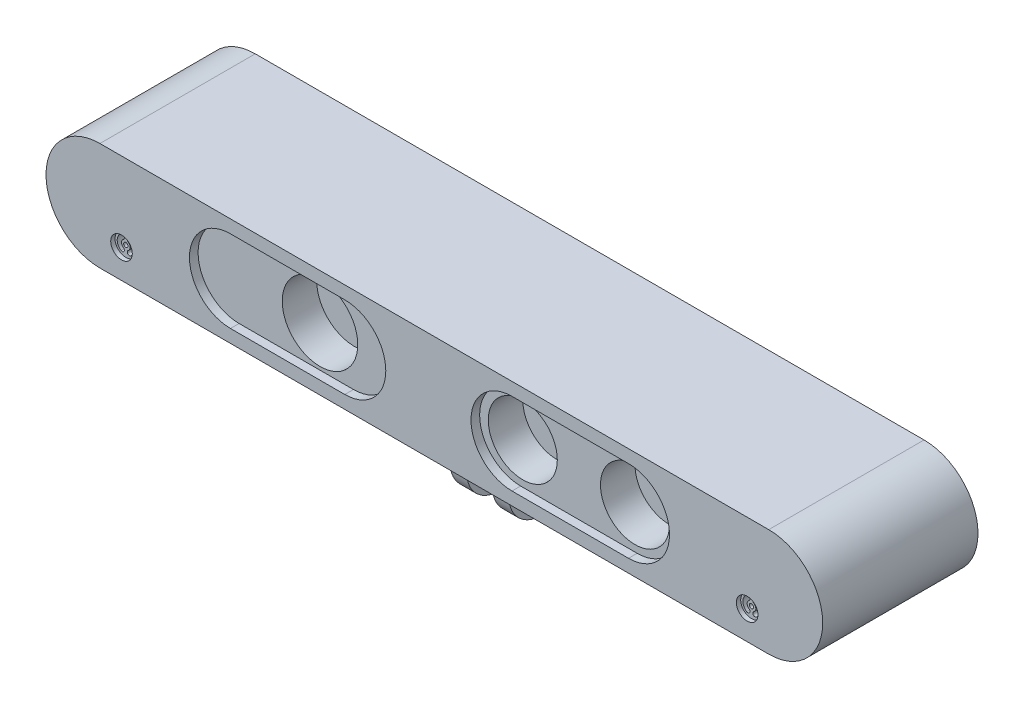
SolidWorks part; units mm, degrees
ref_plane "Front Plane" through (0, 0, 0) normal (0, 0, 1) x (1, 0, 0)
ref_plane "Top Plane" through (0, 0, 0) normal (0, 1, 0) x (1, 0, 0)
ref_plane "Right Plane" through (0, 0, 0) normal (1, 0, 0) x (0, 0, -1)
sketch "Sketch1" plane through (0, 0, 0) normal (0, 0, 1) x (1, 0, 0)
  line L0 (-77.5, 0) -> (77.5, 0) construction
  line L1 (-77.5, 12.5) -> (77.5, 12.5)
  line L2 (-77.5, -12.5) -> (77.5, -12.5)
  arc A0 (-77.5, 12.5) -> (-77.5, -12.5) centre (-77.5, 0) ccw
  arc A1 (77.5, -12.5) -> (77.5, 12.5) centre (77.5, 0) ccw
  point P3 (0, 0)
  dimension "D1" = 12.5
  dimension "D3" = 0
  dimension "D2" = 155
extrude "Boss-Extrude1" add sketch "Sketch1" against normal blind 36
sketch "Sketch3" plane through (0, 0, 0) normal (0, 0, 1) x (1, 0, 0)
  circle A0 centre (-28.5, 0) radius 8.75
  circle A1 centre (18.5, 0) radius 8
  circle A2 centre (44.5, 0) radius 8
  dimension "D1" = 17.5
  dimension "D4" = 16
  dimension "D7" = 16
  dimension "D2" = 28.5
  dimension "D3" = 0
  dimension "D5" = 47
  dimension "D6" = 73
  dimension "D8" = 0
  dimension "D9" = 0
extrude "Cut-Extrude1" cut sketch "Sketch3" against normal blind 10
sketch "Sketch4" plane through (0, 0, 0) normal (0, 0, 1) x (1, 0, 0)
  line L0 (-47.25, 0) -> (-20.75, 0) construction
  line L1 (-47.25, 9.5) -> (-20.75, 9.5)
  line L2 (-47.25, -9.5) -> (-20.75, -9.5)
  line L3 (18, 0) -> (45, 0) construction
  line L4 (18, 9.5) -> (45, 9.5)
  line L5 (18, -9.5) -> (45, -9.5)
  arc A0 (-47.25, 9.5) -> (-47.25, -9.5) centre (-47.25, 0) ccw
  arc A1 (-20.75, -9.5) -> (-20.75, 9.5) centre (-20.75, 0) ccw
  arc A2 (18, 9.5) -> (18, -9.5) centre (18, 0) ccw
  arc A3 (45, -9.5) -> (45, 9.5) centre (45, 0) ccw
  point P3 (-34, 0)
  point P8 (31.5, 0)
  dimension "D1" = 9.5
  dimension "D2" = 9.5
  dimension "D6" = 31.5
  dimension "D3" = 26.5
  dimension "D4" = 34
  dimension "D5" = 27
extrude "Cut-Extrude2" cut sketch "Sketch4" against normal blind 2
sketch "Sketch5" plane through (0, 0, 0) normal (0, 0, 1) x (1, 0, 0)
  circle A0 centre (72.5, -5.8596) radius 2.5
  circle A1 centre (-72.5, -5.8596) radius 2.5
  dimension "D1" = 5
  dimension "D2" = 5
  dimension "D3" = 72.5
  dimension "D4" = 72.5
extrude "Cut-Extrude3" cut sketch "Sketch5" against normal blind 1
sketch "Sketch6" plane through (0, 0, 0) normal (0, 0, 1) x (1, 0, 0)
  circle A0 centre (-72.5, -5.8596) radius 0.5
  circle A1 centre (72.5, -5.8596) radius 0.5
  arc A2 (-71.6708, -4.6096) -> (-71.6708, -7.1096) centre (-72.5, -5.8596) cw construction
  arc A3 (-71.3945, -7.5262) -> (-71.3945, -4.1929) centre (-72.5, -5.8596) ccw
  arc A4 (-71.9472, -6.6929) -> (-71.9472, -5.0262) centre (-72.5, -5.8596) ccw
  arc A5 (-71.9472, -6.6929) -> (-71.3945, -7.5262) centre (-71.6708, -7.1096) ccw
  arc A6 (-71.3945, -4.1929) -> (-71.9472, -5.0262) centre (-71.6708, -4.6096) ccw
  arc A7 (-73.3292, -4.6096) -> (-73.3292, -7.1096) centre (-72.5, -5.8596) ccw construction
  arc A8 (-73.6055, -4.1929) -> (-73.6055, -7.5262) centre (-72.5, -5.8596) ccw
  arc A9 (-73.0528, -5.0262) -> (-73.0528, -6.6929) centre (-72.5, -5.8596) ccw
  arc A10 (-73.0528, -5.0262) -> (-73.6055, -4.1929) centre (-73.3292, -4.6096) ccw
  arc A11 (-73.6055, -7.5262) -> (-73.0528, -6.6929) centre (-73.3292, -7.1096) ccw
  arc A12 (73.3292, -4.6096) -> (73.3292, -7.1096) centre (72.5, -5.8596) cw construction
  arc A13 (73.6055, -7.5262) -> (73.6055, -4.1929) centre (72.5, -5.8596) ccw
  arc A14 (73.0528, -6.6929) -> (73.0528, -5.0262) centre (72.5, -5.8596) ccw
  arc A15 (73.0528, -6.6929) -> (73.6055, -7.5262) centre (73.3292, -7.1096) ccw
  arc A16 (73.6055, -4.1929) -> (73.0528, -5.0262) centre (73.3292, -4.6096) ccw
  arc A17 (71.6708, -4.6096) -> (71.6708, -7.1096) centre (72.5, -5.8596) ccw construction
  arc A18 (71.3945, -4.1929) -> (71.3945, -7.5262) centre (72.5, -5.8596) ccw
  arc A19 (71.9472, -5.0262) -> (71.9472, -6.6929) centre (72.5, -5.8596) ccw
  arc A20 (71.9472, -5.0262) -> (71.3945, -4.1929) centre (71.6708, -4.6096) ccw
  arc A21 (71.3945, -7.5262) -> (71.9472, -6.6929) centre (71.6708, -7.1096) ccw
  circle A22 centre (72.5, -5.8596) radius 2.5 construction
  point P8 (-71, -5.8596)
  point P16 (-74, -5.8596)
  point P23 (74, -5.8596)
  point P31 (71, -5.8596)
  dimension "D2" = 1
  dimension "D5" = 0.5
  dimension "D6" = 2.5
  dimension "D9" = 0.5
  dimension "D11" = 1
  dimension "D14" = 0.5
  dimension "D18" = 0.5
  dimension "D3" = 0
  dimension "D4" = 1.5
  dimension "D7" = 0
  dimension "D8" = 2.5
  dimension "D10" = 1.5
  dimension "D12" = 0
  dimension "D13" = 1.5
  dimension "D15" = 2.5
  dimension "D16" = 0
  dimension "D17" = 2.5
  dimension "D19" = 1.5
  dimension "D21" = 0
extrude "Cut-Extrude4" cut sketch "Sketch6" against normal blind 5
sketch "Sketch7" plane through (0, -12.5, 0) normal (0, -1, 0) x (1, 0, 0)
  line L0 (-77.5, 0) -> (77.5, 0) construction
  line L1 (3, -10.5) -> (6.8, -10.5)
  line L2 (3, -10.5) -> (3, -25.5)
  line L3 (3, -25.5) -> (6.8, -25.5)
  line L4 (6.8, -10.5) -> (6.8, -25.5)
  line L6 (-3, -10.5) -> (-6.8, -10.5)
  line L7 (-3, -10.5) -> (-3, -25.5)
  line L8 (-3, -25.5) -> (-6.8, -25.5)
  line L9 (-6.8, -10.5) -> (-6.8, -25.5)
  dimension "D1" = 3.8
  dimension "D2" = 15
  dimension "D3" = 10.5
  dimension "D4" = 3
  dimension "D5" = 3.8
  dimension "D6" = 15
  dimension "D7" = 3
  dimension "D8" = 10.5
extrude "Boss-Extrude2" add sketch "Sketch7" along normal blind 17
sketch "Sketch8" plane through (-6.8, 0, 0) normal (-1, 0, 0) x (0, 0, 1)
  line L0 (-10.5, -29.5) -> (-10.5, -12.5) construction
  line L1 (-25.5, -29.5) -> (-25.5, -12.5) construction
  line L2 (-10.5, -21) -> (-7.9034, -21)
  line L3 (-7.9034, -21) -> (-7.606, -33.9286)
  line L4 (-7.606, -33.9286) -> (-27.6037, -34.3885)
  line L5 (-27.6037, -34.3885) -> (-27.6037, -21)
  line L6 (-27.6037, -21) -> (-25.5, -21)
  arc A0 (-10.5, -21) -> (-25.5, -21) centre (-18, -21.4844) cw
  circle A1 centre (-18, -21.4844) radius 2.5
extrude "Cut-Extrude5" cut sketch "Sketch8" along normal through all and the other way through all
